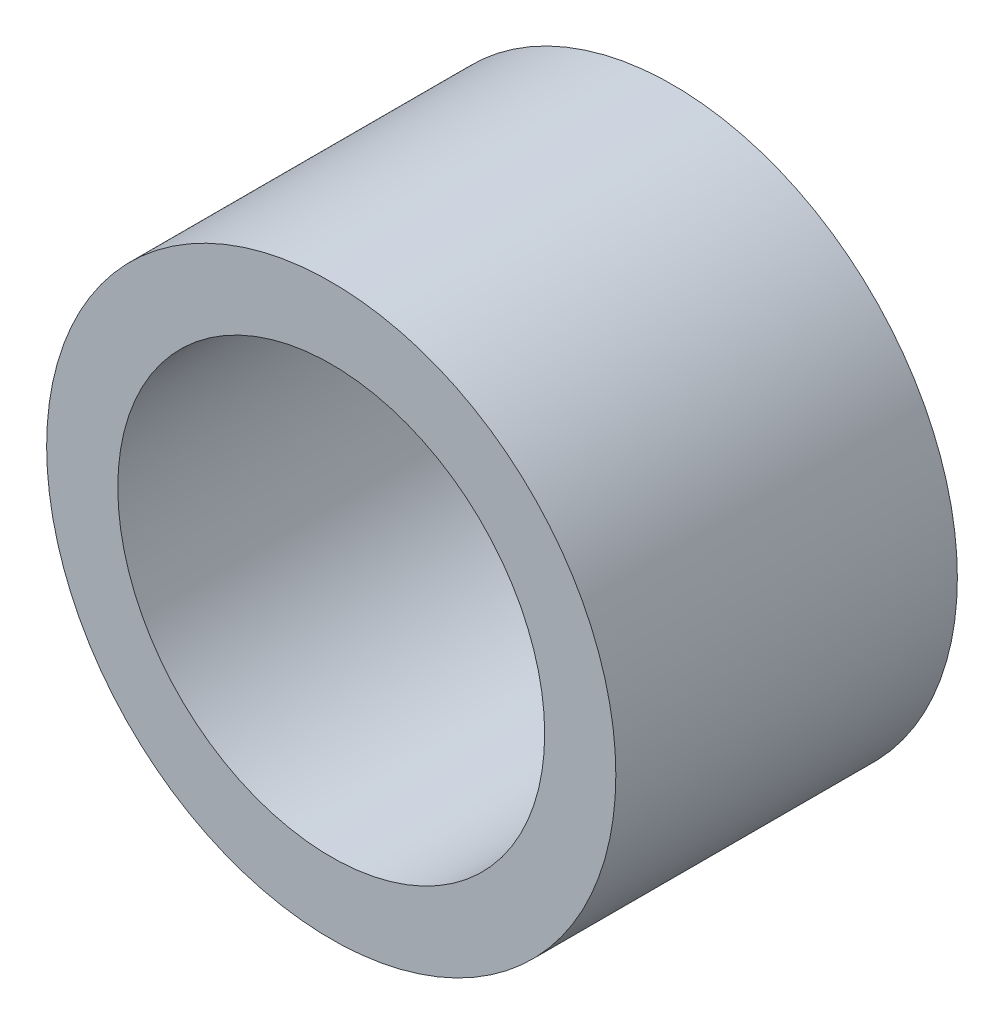
SolidWorks part; units mm, degrees
ref_plane "Front Plane" through (0, 0, 0) normal (0, 0, 1) x (1, 0, 0)
ref_plane "Top Plane" through (0, 0, 0) normal (0, 1, 0) x (1, 0, 0)
ref_plane "Right Plane" through (0, 0, 0) normal (1, 0, 0) x (0, 0, -1)
sketch "Sketch2" plane through (0, 0, 0) normal (0, 0, 1) x (1, 0, 0)
  circle A0 centre (0, 0) radius 3.175
  circle A1 centre (0, 0) radius 4.2333
  dimension "D1" = 6.35
  dimension "D2" = 8.4667
extrude "Boss-Extrude1" add sketch "Sketch2" along normal blind 5.08
